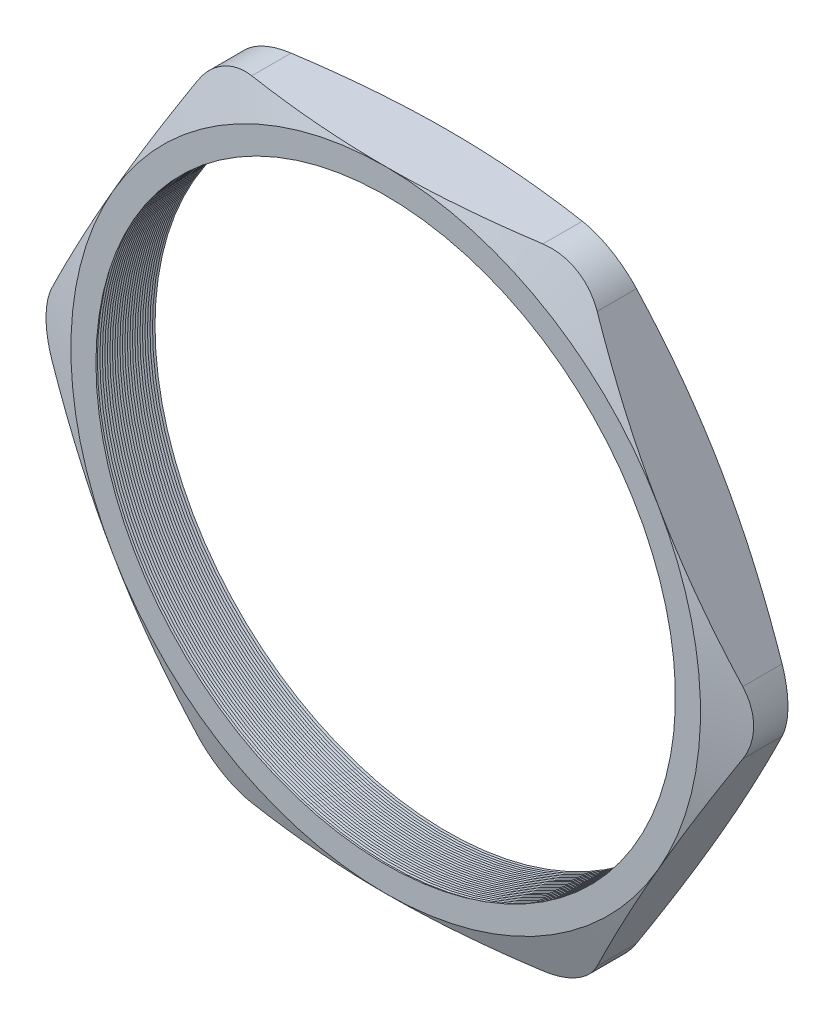
SolidWorks part; units mm, degrees
ref_plane "Front Plane" through (0, 0, 0) normal (0, 0, 1) x (1, 0, 0)
ref_plane "Top Plane" through (0, 0, 0) normal (0, 1, 0) x (1, 0, 0)
ref_plane "Right Plane" through (0, 0, 0) normal (1, 0, 0) x (0, 0, -1)
sketch "Sketch1" plane through (0, 0, 0) normal (0, 0, 1) x (1, 0, 0)
  line L1 (-29.476, 0) -> (-14.738, -25.527)
  line L2 (-14.738, -25.527) -> (14.738, -25.527)
  line L3 (14.738, -25.527) -> (29.476, 0)
  line L4 (29.476, 0) -> (14.738, 25.527)
  line L5 (14.738, 25.527) -> (-14.738, 25.527)
  line L6 (-14.738, 25.527) -> (-29.476, 0)
  circle A0 centre (0, 0) radius 25.527 construction
  circle A1 centre (0, 0) radius 23.495
  dimension "TS" = 46.99
  dimension "H" = 51.054
extrude "Extrude1" add sketch "Sketch1" along normal blind 5.08
fillet "Fillet1" radius 5.08 6 edges at (-14.738, 25.527, 2.54) (-29.476, 0, 2.54) (-14.738, -25.527, 2.54) (14.738, -25.527, 2.54) (29.476, 0, 2.54) (14.738, 25.527, 2.54)
sketch "Sketch2" plane through (0, 0, 5.08) normal (0, 0, 1) x (1, 0, 0)
  line L0 (11.8051, 25.527) -> (-11.8051, 25.527) construction
  circle A0 centre (0, 0) radius 25.527
extrude "Cut-Extrude1" cut sketch "Sketch2" against normal through all draft 70 flip side to cut
sketch "Sketch3" plane through (0, 0, 0) normal (0, 0, -1) x (-1, 0, 0)
  circle A0 centre (0, 0) radius 25.527
extrude "Cut-Extrude2" cut sketch "Sketch3" against normal through all draft 70 flip side to cut
sketch "Sketch4" plane through (0, 0, 0) normal (0, 1, 0) x (1, 0, 0)
  line L0 (-23.495, -5.08) -> (-23.495, -4.6401)
  line L2 (-23.495, -4.6401) -> (-23.876, -4.86)
  line L3 (-23.876, -4.86) -> (-23.495, -5.08)
  line L5 (-23.495, 0) -> (-23.495, -5.08) construction
  line L6 (-23.495, -5.08) -> (23.495, -5.08) construction
  dimension "D1" = 60
  dimension "D2" = 60
  dimension "D3" = 0.381
revolve "Cut-Revolve1" cut sketch "Sketch4" angle 360 about axis through (0, 0, 5.08) along (0, 0, -1)
pattern_linear "LPattern1" count 25 spacing 0.2032 along (0, 0, -1) of "Cut-Revolve1"
